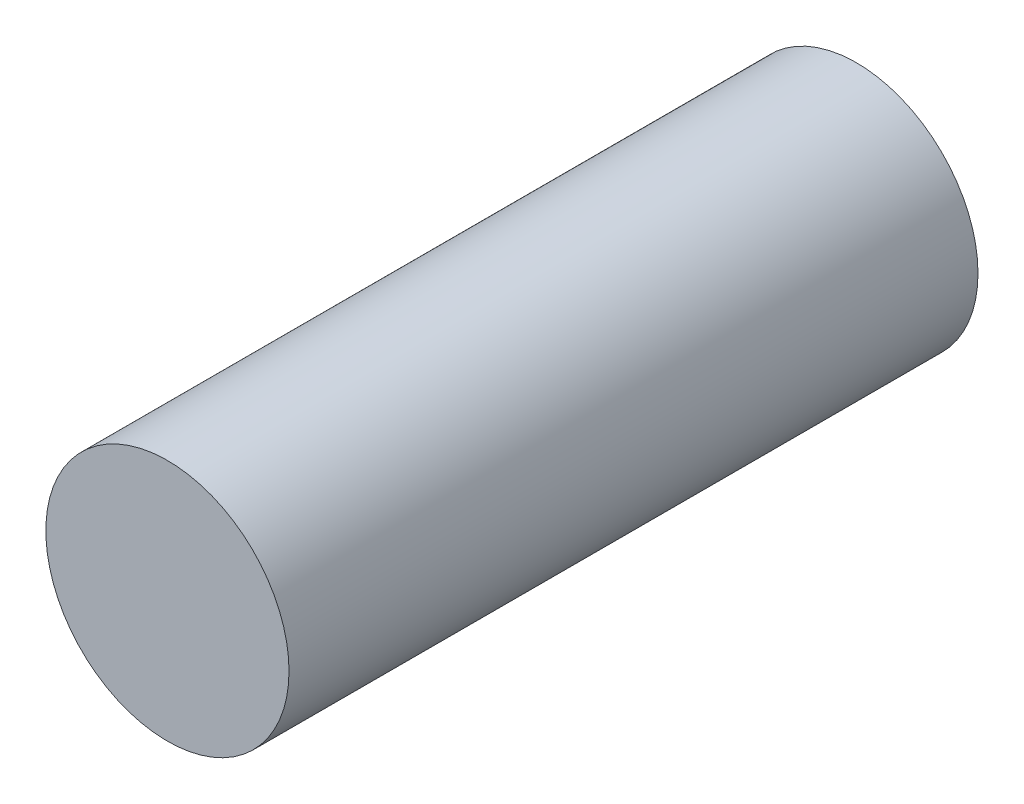
SolidWorks part; units mm, degrees
ref_plane "正面" through (0, 0, 0) normal (0, 0, 1) x (1, 0, 0)
ref_plane "平面" through (0, 0, 0) normal (0, 1, 0) x (1, 0, 0)
ref_plane "右側面" through (0, 0, 0) normal (1, 0, 0) x (0, 0, -1)
sketch "ｽｹｯﾁ1" plane through (0, 0, 0) normal (0, 0, 1) x (1, 0, 0)
  circle A0 centre (8, 46) radius 3 construction
  circle A1 centre (8, 46) radius 3
extrude "ﾎﾞｽ - 押し出し1" add sketch "ｽｹｯﾁ1" along normal up to surface (17 mm away)
